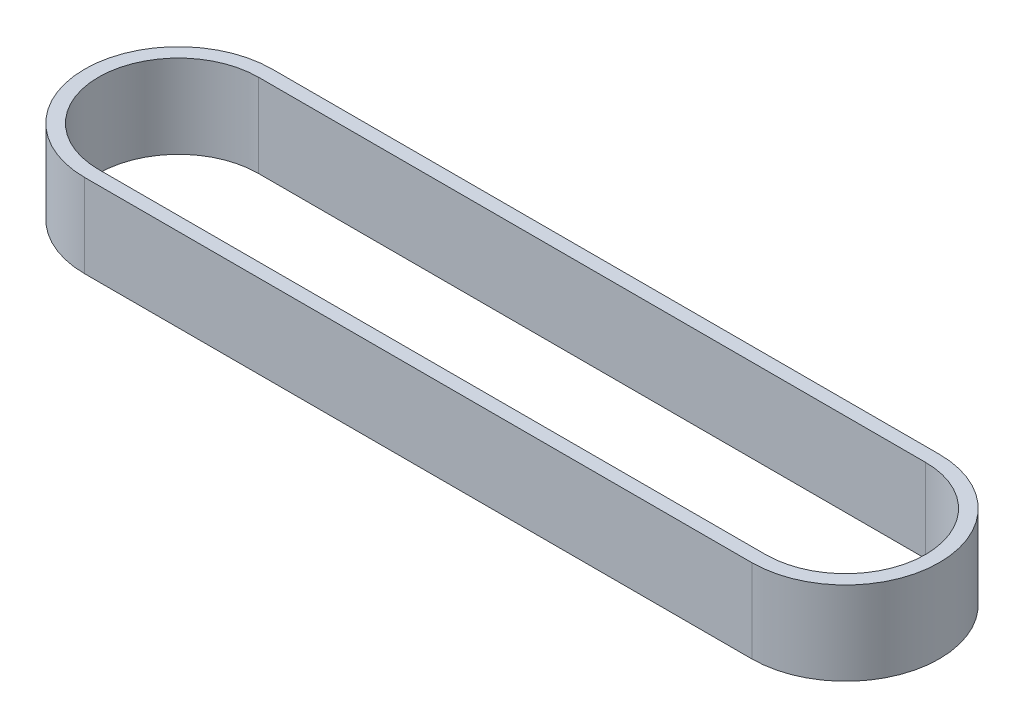
SolidWorks part; units mm, degrees
material "BUTYL"
ref_plane "Front Plane" through (0, 0, 0) normal (0, 0, 1) x (1, 0, 0)
ref_plane "Top Plane" through (0, 0, 0) normal (0, 1, 0) x (1, 0, 0)
ref_plane "Right Plane" through (0, 0, 0) normal (1, 0, 0) x (0, 0, -1)
sketch "Sketch1" plane through (0, 0, 0) normal (0, 1, 0) x (1, 0, 0)
  line L0 (0, 0) -> (48, 0) construction
  line L1 (0, 5.75) -> (48, 5.75)
  line L2 (0, -5.75) -> (48, -5.75)
  line L3 (0, 0) -> (48, 0) construction
  line L4 (0, 6.75) -> (48, 6.75)
  line L5 (0, -6.75) -> (48, -6.75)
  arc A0 (0, 5.75) -> (0, -5.75) centre (0, 0) ccw
  arc A1 (48, -5.75) -> (48, 5.75) centre (48, 0) ccw
  arc A2 (0, 6.75) -> (0, -6.75) centre (0, 0) ccw
  arc A3 (48, -6.75) -> (48, 6.75) centre (48, 0) ccw
  point P3 (24, 0)
  point P10 (24, 0)
  dimension "D1" = 5.75
  dimension "D2" = 1
  dimension "D3" = 48
extrude "Boss-Extrude1" add sketch "Sketch1" along normal blind 6
